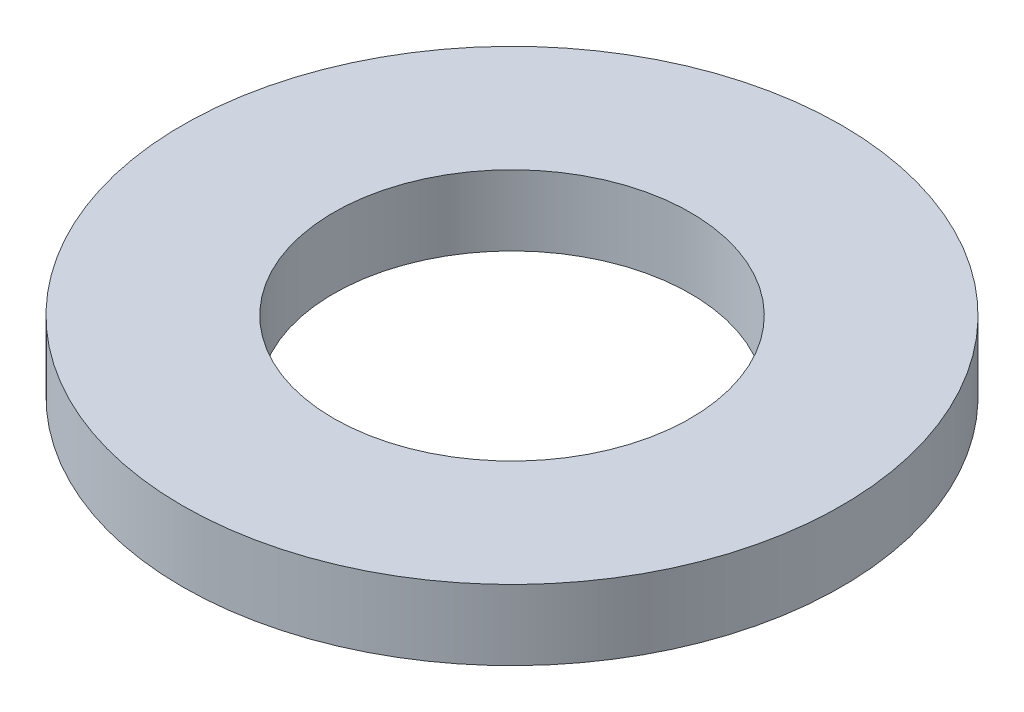
SolidWorks part; units mm, degrees
material "Plain Carbon Steel"
ref_plane "Front Plane" through (0, 0, 0) normal (0, 0, 1) x (1, 0, 0)
ref_plane "Top Plane" through (0, 0, 0) normal (0, 1, 0) x (1, 0, 0)
ref_plane "Right Plane" through (0, 0, 0) normal (1, 0, 0) x (0, 0, -1)
sketch "Sketch1" plane through (0, 0, 0) normal (0, 1, 0) x (1, 0, 0)
  circle A0 centre (0, 0) radius 9.525
  dimension "OD" = 19.05
extrude "Boss-Extrude1" add sketch "Sketch1" along normal blind 2.032
sketch "Sketch5" plane through (0, 2.032, 0) normal (0, 1, 0) x (-1, 0, 0)
  circle A0 centre (0, 0) radius 5.1562
  dimension "ID" = 10.3124
extrude "Cut-Extrude1" cut sketch "Sketch5" against normal through all
